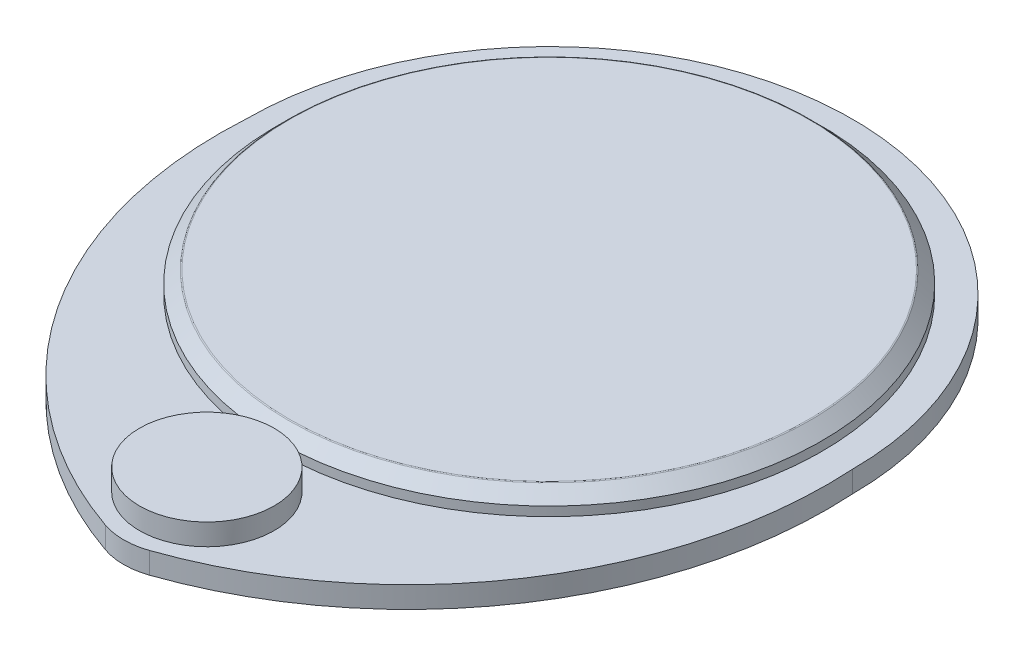
SolidWorks part; units mm, degrees
material "ABS"
ref_plane "Front Plane" through (0, 0, 0) normal (0, 0, 1) x (1, 0, 0)
ref_plane "Top Plane" through (0, 0, 0) normal (0, 1, 0) x (1, 0, 0)
ref_plane "Right Plane" through (0, 0, 0) normal (1, 0, 0) x (0, 0, -1)
sketch "Sketch1" plane through (0, 0, 0) normal (0, 1, 0) x (1, 0, 0)
  circle A0 centre (0, 0) radius 44.5
  dimension "D1" = 89
extrude "Boss-Extrude1" add sketch "Sketch1" along normal blind 3.5
chamfer "Chamfer1" distance 2 1 edges at (0, 3.5, 44.5)
sketch "Sketch2" plane through (0, 0, 0) normal (0, -1, 0) x (1, 0, 0)
  circle A0 centre (0, 0) radius 49.5
  dimension "D1" = 99
extrude "Boss-Extrude2" add sketch "Sketch2" along normal blind 3.5 contours A0
sketch "Sketch3" plane through (0, 0, 0) normal (0, 1, 0) x (1, 0, 0)
  line L0 (0, -3.85) -> (0, 3.85) construction
  arc A0 (49.5, 0) -> (0, -70) centre (-18.8432, -4.1734) cw
  circle A1 centre (0, 0) radius 49.5 construction
  arc A2 (-49.5, 0) -> (0, -70) centre (18.8432, -4.1734) ccw
  arc A3 (-49.5, 0) -> (49.5, 0) centre (0, 0) ccw
  dimension "D1" = 70
extrude "Boss-Extrude3" add sketch "Sketch3" against normal blind 3.5
sketch "Sketch7" plane through (0, 0, 0) normal (0, 1, 0) x (1, 0, 0)
  circle A0 centre (0, -55.892) radius 10.9917
extrude "Boss-Extrude4" add sketch "Sketch7" along normal blind 3.5
fillet "Fillet1" radius 11 1 edges at (0, -1.75, 70)
fillet "Fillet2" radius 0.25 1 edges at (0, 3.5, 42.5)
sketch "Sketch8" plane through (0, 3.5, 0) normal (0, 1, 0) x (1, 0, 0)
  line L0 (0, -66.8837) -> (0, -44.9003) construction
  circle A0 centre (0, -55.892) radius 10.9917 construction
  circle A1 centre (0, -55.892) radius 10.9917 construction
